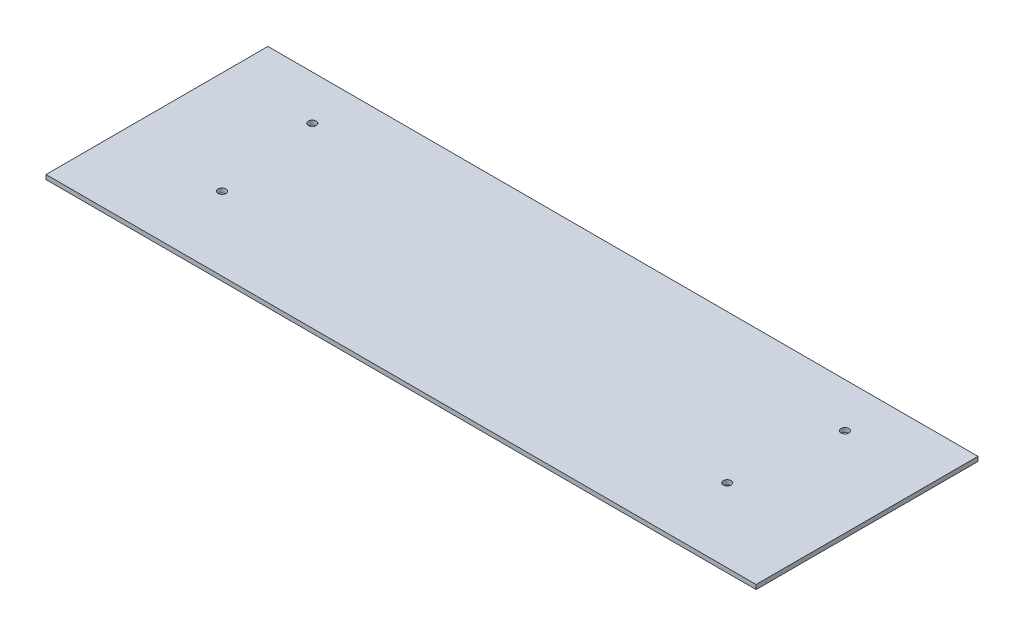
SolidWorks part; units mm, degrees
ref_plane "Front Plane" through (0, 0, 0) normal (0, 0, 1) x (1, 0, 0)
ref_plane "Top Plane" through (0, 0, 0) normal (0, 1, 0) x (1, 0, 0)
ref_plane "Right Plane" through (0, 0, 0) normal (1, 0, 0) x (0, 0, -1)
sketch "Sketch1" plane through (0, 0, 0) normal (0, 1, 0) x (1, 0, 0)
  line L0 (152.4, 38.1) -> (-152.4, 38.1)
  line L1 (203.2, -63.5) -> (-203.2, -63.5)
  line L2 (203.2, -63.5) -> (203.2, 63.5)
  line L3 (203.2, 63.5) -> (-203.2, 63.5)
  line L4 (-203.2, -63.5) -> (-203.2, 63.5)
  line L5 (203.2, -63.5) -> (-203.2, 63.5) construction
  line L6 (203.2, 63.5) -> (-203.2, -63.5) construction
  line L7 (0, 63.5) -> (0, -63.5) construction
  line L8 (-152.4, 38.1) -> (-152.4, -63.5) construction
  line L9 (152.4, 38.1) -> (152.4, -63.5) construction
  line L10 (152.4, 38.1) -> (146.9689, -3.1534) construction
  line L11 (-152.4, 38.1) -> (-149.146, 13.3837) construction
  circle A0 centre (-152.4, 38.1) radius 2.25
  circle A1 centre (152.4, 38.1) radius 2.25
  circle A2 centre (144.5684, -21.3867) radius 2.25
  circle A3 centre (-144.5684, -21.3867) radius 2.25
  point P0 (0, 0)
  point P9 (0, 0)
  dimension "D4" = 4.5
  dimension "D1" = 127
  dimension "D2" = 406.4
  dimension "D3" = 304.8
  dimension "D5" = 25.4
  dimension "D6" = 7.5
  dimension "D7" = 7.5
  dimension "D8" = 60
  dimension "D9" = 60
extrude "Boss-Extrude1" add sketch "Sketch1" along normal blind 2.54
